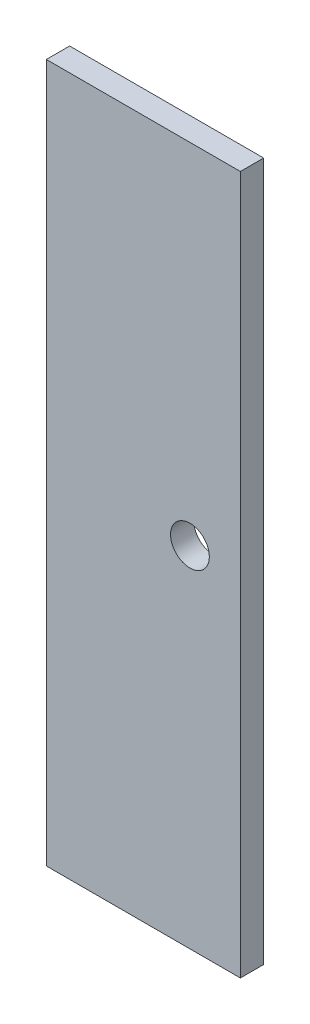
SolidWorks part; units mm, degrees
ref_plane "Alzado" through (0, 0, 0) normal (0, 0, 1) x (1, 0, 0)
ref_plane "Planta" through (0, 0, 0) normal (0, 1, 0) x (1, 0, 0)
ref_plane "Vista lateral" through (0, 0, 0) normal (1, 0, 0) x (0, 0, -1)
sketch "Croquis1" plane through (0, 0, 0) normal (0, 0, 1) x (1, 0, 0)
  line L1 (25, -90) -> (-25, -90)
  line L2 (25, -90) -> (25, 90)
  line L3 (25, 90) -> (-25, 90)
  line L4 (-25, -90) -> (-25, 90)
  line L5 (25, -90) -> (-25, 90) construction
  line L6 (25, 90) -> (-25, -90) construction
  point P0 (0, 0)
  dimension "D1" = 180
  dimension "D2" = 50
extrude "Saliente-Extruir1" add sketch "Croquis1" along normal blind 6
sketch "Croquis2" plane through (0, 0, 6) normal (0, 0, 1) x (1, 0, 0)
  line L0 (-25, 0) -> (12, 0) construction
  line L1 (-25, 90) -> (-25, -90) construction
  circle A0 centre (12, 0) radius 5
  dimension "D1" = 10
  dimension "D2" = 12
extrude "Cortar-Extruir1" cut sketch "Croquis2" against normal blind 10
